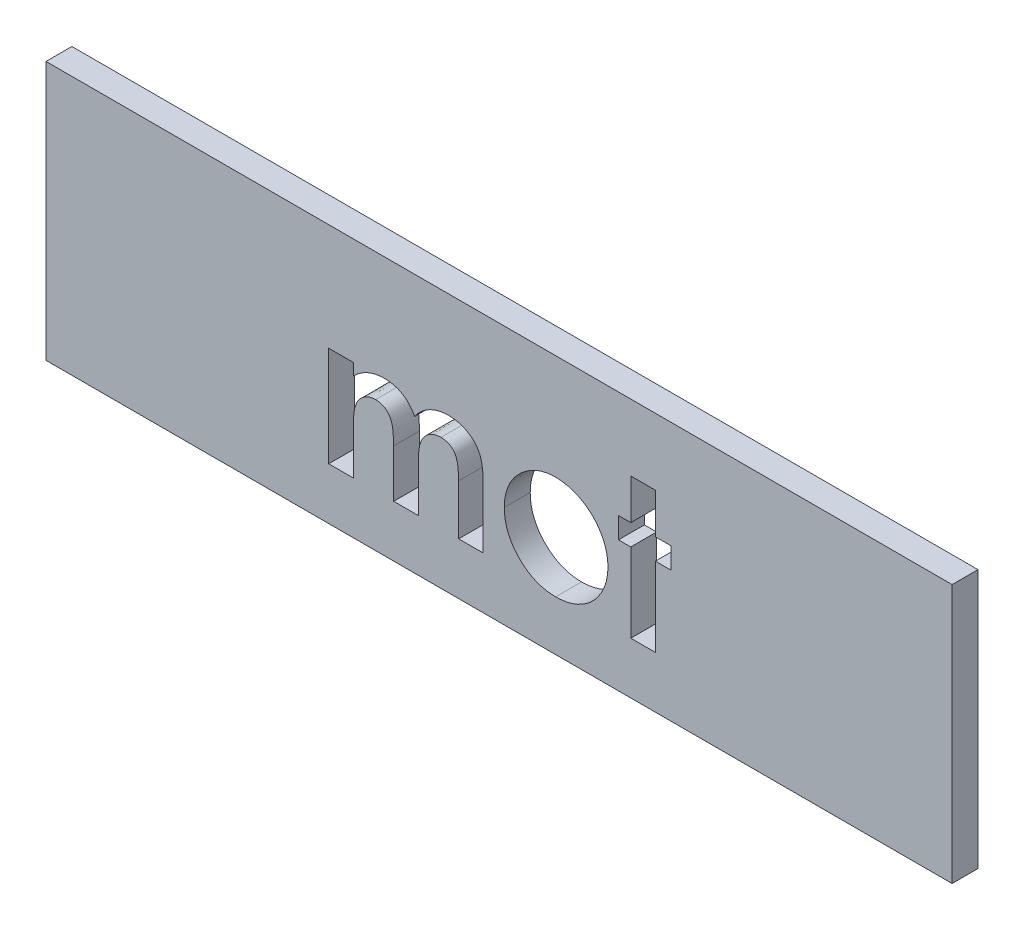
SolidWorks part; units mm, degrees
ref_plane "Plan de face" through (0, 0, 0) normal (0, 0, 1) x (1, 0, 0)
ref_plane "Plan de dessus" through (0, 0, 0) normal (0, 1, 0) x (1, 0, 0)
ref_plane "Plan de droite" through (0, 0, 0) normal (1, 0, 0) x (0, 0, -1)
sketch "Esquisse1" plane through (0, 0, 0) normal (0, 0, 1) x (1, 0, 0)
  line L1 (0, 0) -> (35, 0)
  line L2 (0, 0) -> (0, -10)
  line L3 (0, -10) -> (35, -10)
  line L4 (35, 0) -> (35, -10)
  dimension "D1" = 35
  dimension "D2" = 10
extrude "Boss.-Extru.1" add sketch "Esquisse1" along normal blind 1
sketch "Esquisse2" plane through (0, 0, 0) normal (0, 0, -1) x (-1, 0, 0)
  line L0 (-35, 0) -> (0, 0) construction
  line L1 (-35, -10) -> (-35, 0) construction
  line L2 (0, 0) -> (0, -10) construction
  circle A0 centre (-30, -5) radius 1
  circle A1 centre (-5, -5) radius 1
  dimension "D4" = 2
  dimension "D1" = 5
  dimension "D2" = 5
  dimension "D3" = 5
extrude "Boss.-Extru.2" add sketch "Esquisse2" along normal blind 3
chamfer "Chanfrein1" distance 0.5 angle 45 2 edges at (29, -5, -3) (4, -5, -3)
sketch "Esquisse3" plane through (0, 0, 1) normal (0, 0, 1) x (1, 0, 0)
  line L0 (7.5, -8) -> (27.5, -8) construction
  line L3 (0, -10) -> (35, -10) construction
  line L4 (0, 0) -> (0, -10) construction
  line L5 (35, -10) -> (35, 0) construction
  text T1 "<b>mot</b>" font "Century Gothic" height in points 20
  point P12 (27.5, -8)
  dimension "D1" = 2
  dimension "D2" = 7.5
  dimension "D3" = 20
  dimension "D4" = 7.5
extrude "Enlèv. mat.-Extru.2" cut sketch "Esquisse3" against normal blind 1
